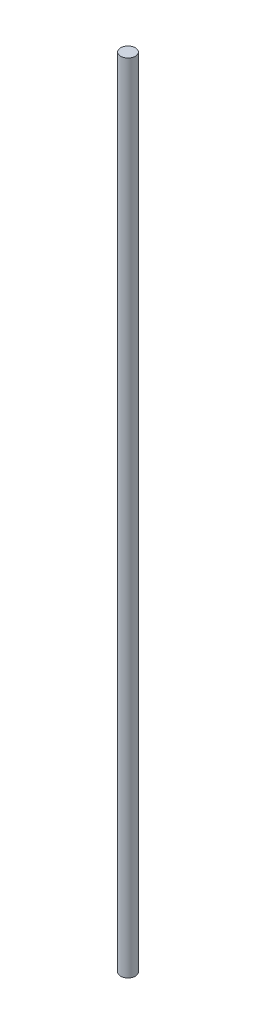
SolidWorks part; units mm, degrees
ref_plane "Front Plane" through (0, 0, 0) normal (0, 0, 1) x (1, 0, 0)
ref_plane "Top Plane" through (0, 0, 0) normal (0, 1, 0) x (1, 0, 0)
ref_plane "Right Plane" through (0, 0, 0) normal (1, 0, 0) x (0, 0, -1)
sketch "Sketch3" plane through (0, 0, 0) normal (0, 1, 0) x (1, 0, 0)
  circle A0 centre (0, 0) radius 12
  dimension "D1" = 24
extrude "Boss-Extrude1" add sketch "Sketch3" along normal blind 1300
